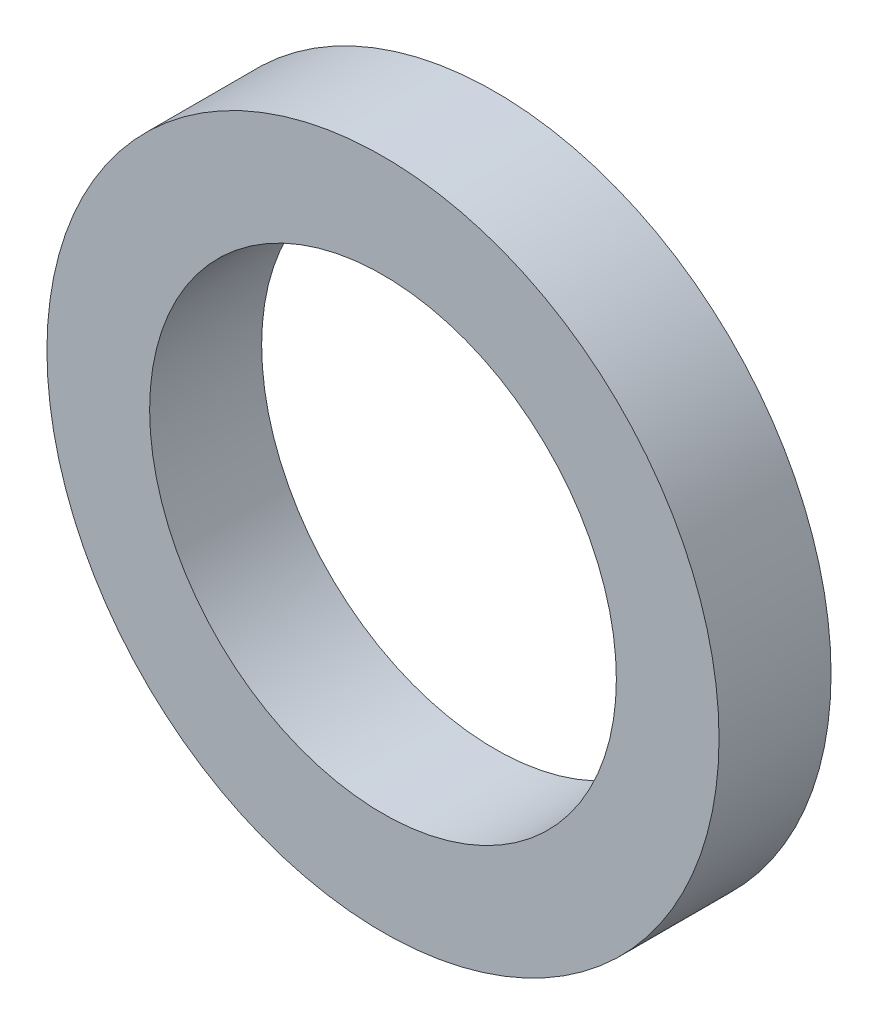
SolidWorks part; units mm, degrees
material "A3钢"
ref_plane "前视基准面" through (0, 0, 0) normal (0, 0, 1) x (1, 0, 0)
ref_plane "上视基准面" through (0, 0, 0) normal (0, 1, 0) x (1, 0, 0)
ref_plane "右视基准面" through (0, 0, 0) normal (1, 0, 0) x (0, 0, -1)
sketch "草图1" plane through (0, 0, 0) normal (0, 0, 1) x (1, 0, 0)
  circle A0 centre (0, 0) radius 9
  circle A1 centre (0, 0) radius 6.25
  dimension "D1" = 12.5
  dimension "D2" = 18
extrude "凸台-拉伸1" add sketch "草图1" along normal blind 3
